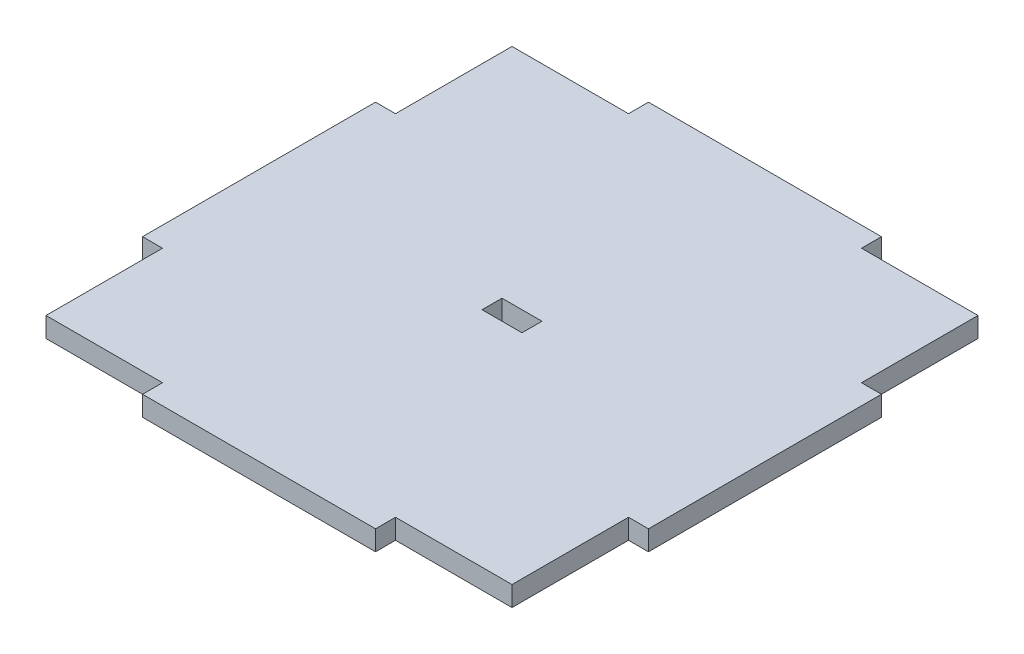
SolidWorks part; units mm, degrees
ref_plane "Front Plane" through (0, 0, 0) normal (0, 0, 1) x (1, 0, 0)
ref_plane "Top Plane" through (0, 0, 0) normal (0, 1, 0) x (1, 0, 0)
ref_plane "Right Plane" through (0, 0, 0) normal (1, 0, 0) x (0, 0, -1)
sketch "Sketch1" plane through (0, 0, 0) normal (0, 1, 0) x (1, 0, 0)
  line L0 (0, 35) -> (0, -35) construction
  line L1 (-35, -35) -> (-17.5, -35)
  line L2 (-35, -35) -> (-35, -17.5)
  line L3 (-35, 35) -> (-17.5, 35)
  line L4 (35, -35) -> (35, -17.5)
  line L5 (-35, -35) -> (35, 35) construction
  line L6 (-35, 35) -> (35, -35) construction
  line L11 (-38, -38) -> (38, 38) construction
  line L12 (-38, 38) -> (38, -38) construction
  line L13 (-35, 0) -> (35, 0) construction
  line L14 (-17.5, 38) -> (-17.5, 35)
  line L15 (-38, 17.5) -> (-35, 17.5)
  line L16 (17.5, 38) -> (17.5, 35)
  line L17 (-38, -17.5) -> (-35, -17.5)
  line L18 (38, 17.5) -> (35, 17.5)
  line L19 (38, -17.5) -> (35, -17.5)
  line L20 (17.5, -38) -> (17.5, -35)
  line L21 (-17.5, -38) -> (-17.5, -35)
  line L22 (-38, -17.5) -> (-38, 17.5)
  line L23 (38, 17.5) -> (38, -17.5)
  line L24 (-17.5, -38) -> (17.5, -38)
  line L25 (-17.5, 38) -> (17.5, 38)
  line L26 (17.5, 35) -> (35, 35)
  line L27 (35, 17.5) -> (35, 35)
  line L28 (17.5, -35) -> (35, -35)
  line L29 (-35, 17.5) -> (-35, 35)
  point P0 (0, 0)
  point P6 (0, 0)
  dimension "D1" = 76
  dimension "D2" = 70
  dimension "D3" = 76
  dimension "D4" = 70
  dimension "D5" = 17.5
  dimension "D6" = 17.5
  dimension "D7" = 3
  dimension "D8" = 3
extrude "Boss-Extrude1" add sketch "Sketch1" along normal blind 3
sketch "Sketch2" plane through (0, 3, 0) normal (0, 1, 0) x (1, 0, 0)
  line L1 (-3, -1.5) -> (3, -1.5)
  line L2 (-3, -1.5) -> (-3, 1.5)
  line L3 (-3, 1.5) -> (3, 1.5)
  line L4 (3, -1.5) -> (3, 1.5)
  line L5 (-3, -1.5) -> (3, 1.5) construction
  line L6 (-3, 1.5) -> (3, -1.5) construction
  point P0 (0, 0)
  dimension "D1" = 3
  dimension "D2" = 6
extrude "Cut-Extrude1" cut sketch "Sketch2" against normal blind 3
